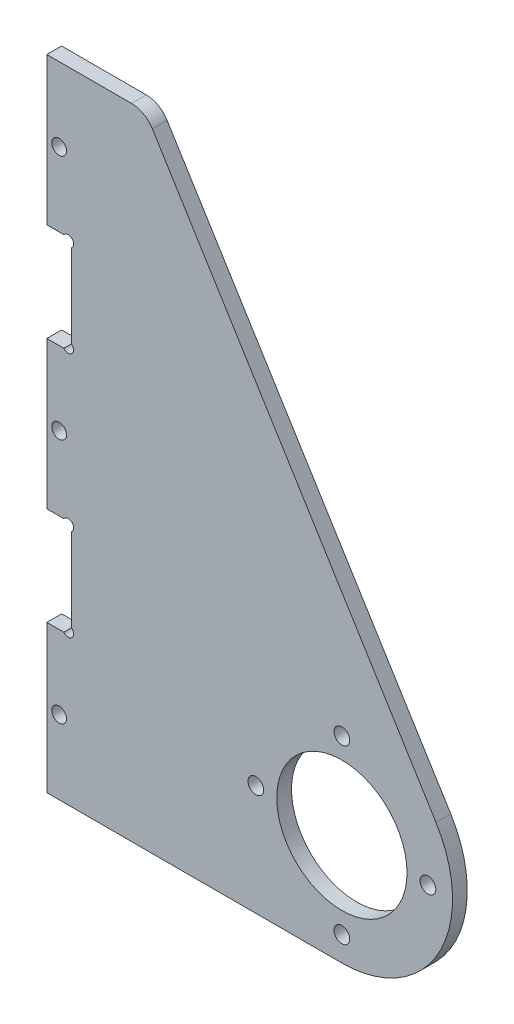
SolidWorks part; units mm, degrees
material "3.1325 (EN-AW 2017A)"
ref_plane "正面" through (0, 0, 0) normal (0, 0, 1) x (1, 0, 0)
ref_plane "平面" through (0, 0, 0) normal (0, 1, 0) x (1, 0, 0)
ref_plane "右側面" through (0, 0, 0) normal (1, 0, 0) x (0, 0, -1)
sketch "ｽｹｯﾁ2" plane through (0, 0, 0) normal (0, 0, 1) x (1, 0, 0)
  line L0 (17.5, 0) -> (-17.5, 0) construction
  line L1 (0, -17.5) -> (0, 17.5) construction
  line L2 (-60, -22.5) -> (-40, -22.5)
  line L5 (-60, 107.5) -> (-60, -22.5)
  line L7 (-60, 107.5) -> (-40, 107.5)
  line L8 (-40, 107.5) -> (-40, -22.5) construction
  line L9 (-40, 107.5) -> (19.1386, 11.8306)
  line L10 (-40, -22.5) -> (0, -22.5)
  line L12 (0, -22.5) -> (-60, -22.5) construction
  line L14 (0, -50) -> (-60, -50) construction
  line L15 (-60, -22.5) -> (-60, -50) construction
  circle A0 centre (0, 0) radius 13.25
  circle A1 centre (0, 17.5) radius 1.6
  circle A2 centre (17.5, 0) radius 1.6
  circle A3 centre (0, -17.5) radius 1.6
  circle A4 centre (-17.5, 0) radius 1.6
  arc A8 (0, -22.5) -> (19.1386, 11.8306) centre (0, 0) ccw
  circle A9 centre (0, 0) radius 50 construction
  point P6 (0, 0)
  point P9 (0, 0)
  dimension "D1" = 26.5
  dimension "D2" = 3.2
  dimension "D3" = 130
  dimension "D8" = 22.5
  dimension "D9" = 20
  dimension "D12" = 100
  dimension "D13" = 60
  dimension "D6" = 90
  dimension "D7" = 35
extrude "ﾎﾞｽ - 押し出し1" add sketch "ｽｹｯﾁ2" along normal blind 3
fillet "ﾌｨﾚｯﾄ3" radius 5 1 edges at (-40, 107.5, 1.5)
sketch "ｽｹｯﾁ4" plane through (0, 0, 3) normal (0, 0, 1) x (1, 0, 0)
  line L0 (-60, 107.5) -> (-60, -22.5) construction
  line L1 (-60, 77.5) -> (-55, 77.5)
  line L2 (-60, 77.5) -> (-60, 57.5)
  line L3 (-60, 57.5) -> (-55, 57.5)
  line L4 (-55, 77.5) -> (-55, 57.5)
  line L6 (-60, 27.5) -> (-55, 27.5)
  line L7 (-60, 27.5) -> (-60, 7.5)
  line L8 (-60, 7.5) -> (-55, 7.5)
  line L9 (-55, 27.5) -> (-55, 7.5)
  line L10 (-42.7874, 107.5) -> (-60, 107.5) construction
  line L11 (-60, -22.5) -> (0, -22.5) construction
  circle A0 centre (-57.5, -7.5) radius 1.5
  circle A1 centre (-57.5, 42.5) radius 1.5
  circle A2 centre (-57.5, 92.5) radius 1.5
  circle A3 centre (-55.66, 26.84) radius 1.1
  circle A4 centre (-55.66, 8.16) radius 1.1
  circle A5 centre (-55.66, 58.16) radius 1.1
  circle A6 centre (-55.66, 76.84) radius 1.1
  line M13 (-60, 107.5) -> (-60, -22.5)
  dimension "D7" = 3
  dimension "D8" = 2.5
  dimension "D9" = 15
  dimension "D11" = 15
  dimension "D12" = 2.2
  dimension "D13" = 0.66
  dimension "D14" = 0.66
  dimension "D15" = 0.66
  dimension "D17" = 0.66
  dimension "D18" = 2.2
  dimension "D19" = 0.66
  dimension "D2" = 30
  dimension "D3" = 30
  dimension "D4" = 20
  dimension "D5" = 5
  dimension "D6" = 5
  dimension "D16" = 2
  dimension "D20" = 30
  dimension "D10" = 3
extrude "ｶｯﾄ - 押し出し1" cut sketch "ｽｹｯﾁ4" against normal blind 10 contours A2 | A6 L1 L3 A5 L4 M13 | A1 | A3 | L8 L7 L6 L9 | A0 | A4
